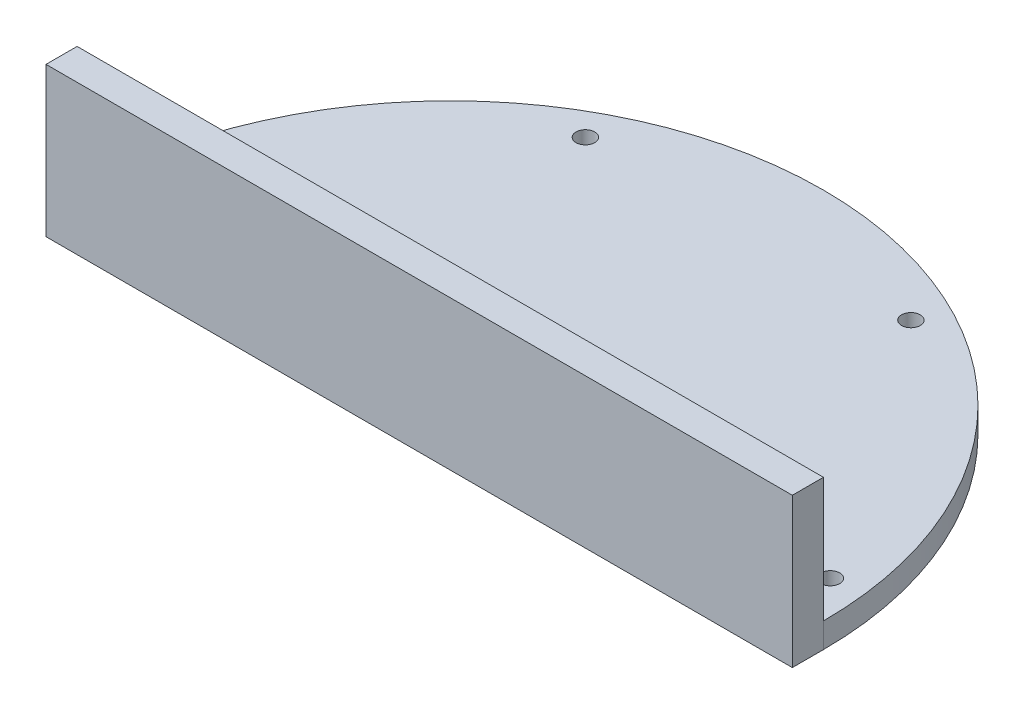
SolidWorks part; units mm, degrees
ref_plane "Front Plane" through (0, 0, 0) normal (0, 0, 1) x (1, 0, 0)
ref_plane "Top Plane" through (0, 0, 0) normal (0, 1, 0) x (1, 0, 0)
ref_plane "Right Plane" through (0, 0, 0) normal (1, 0, 0) x (0, 0, -1)
sketch "Sketch1" plane through (0, 0, 0) normal (0, 1, 0) x (1, 0, 0)
  line L0 (-60, 0) -> (-25.75, 0)
  line L1 (25.75, 0) -> (60, 0)
  line L2 (-25.75, 0) -> (25.75, 0)
  arc A0 (60, 0) -> (-60, 0) centre (0, 0) ccw
  dimension "D2" = 120
extrude "Boss-Extrude1" add sketch "Sketch1" along normal blind 5
sketch "Sketch2" plane through (0, 5, 0) normal (0, 1, 0) x (1, 0, 0)
  circle A0 centre (-54.7723, 5) radius 1.5
  arc A1 (60, 0) -> (-60, 0) centre (0, 0) ccw construction
  dimension "D1" = 3
  dimension "D2" = 5
  dimension "D3" = 55
extrude "Cut-Extrude1" cut sketch "Sketch2" against normal blind 5
pattern_circular "CirPattern1" count 4 every 56 about axis through (0, 0, 0) along (0, 1, 0) of "Cut-Extrude1"
sketch "Sketch9" plane through (0, 0, 0) normal (0, 0, 1) x (1, 0, 0)
  line L1 (-60, 5) -> (60, 5)
  line L2 (-60, 5) -> (-60, -20)
  line L3 (-60, -20) -> (60, -20)
  line L4 (60, 5) -> (60, -20)
  dimension "D1" = 120
  dimension "D2" = 25
extrude "Boss-Extrude5" add sketch "Sketch9" along normal blind 5
mirror "Mirror3" about plane through (0, 5, 0) normal (0, 1, 0) of "Boss-Extrude1", "Cut-Extrude1", "CirPattern1", "Boss-Extrude5"
sketch "Sketch11" plane through (-60, 0, 0) normal (-1, 0, 0) x (0, 0, 1)
  line L0 (5, 30) -> (5, -20) construction
  line L1 (5, 5) -> (-78.5199, 5)
  line L2 (5, 5) -> (5, -23.9397)
  line L3 (5, -23.9397) -> (-78.5199, -23.9397)
  line L4 (-78.5199, 5) -> (-78.5199, -23.9397)
extrude "Cut-Extrude2" cut sketch "Sketch11" against normal blind 150
chamfer "Chamfer1" distance 1 angle 45 8 edges at (-54.7723, 5, -3.5) (25.154, 5, -47.4109) (0, 5, -60) (-60, 5, 2.5) (0, 5, 5) (60, 5, 2.5) (-26.4831, 5, -46.7042) (54.6149, 5, -4.9971)
